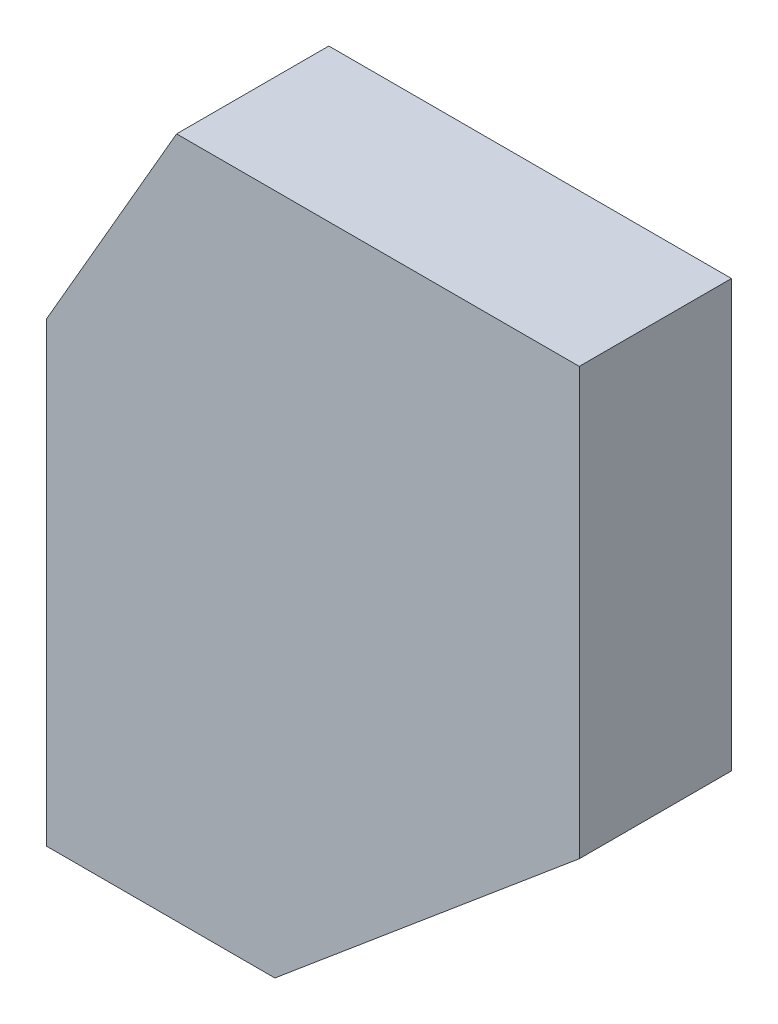
SolidWorks part; units mm, degrees
ref_plane "Front Plane" through (0, 0, 0) normal (0, 0, 1) x (1, 0, 0)
ref_plane "Top Plane" through (0, 0, 0) normal (0, 1, 0) x (1, 0, 0)
ref_plane "Right Plane" through (0, 0, 0) normal (1, 0, 0) x (0, 0, -1)
sketch "Sketch1" plane through (0, 0, 0) normal (0, 0, 1) x (1, 0, 0)
  line L0 (0, 0) -> (19.05, 0)
  line L1 (19.05, 0) -> (44.45, 21.3131)
  line L2 (44.45, 21.3131) -> (44.45, 56.896)
  line L3 (44.45, 56.896) -> (10.8519, 56.896)
  line L4 (10.8519, 56.896) -> (0, 38.1)
  line L5 (0, 38.1) -> (0, 0)
  dimension "D1" = 38.1
  dimension "D2" = 56.896
  dimension "D3" = 30
  dimension "D4" = 40
  dimension "D5" = 19.05
  dimension "D6" = 44.45
extrude "Boss-Extrude1" add sketch "Sketch1" along normal blind 12.7
